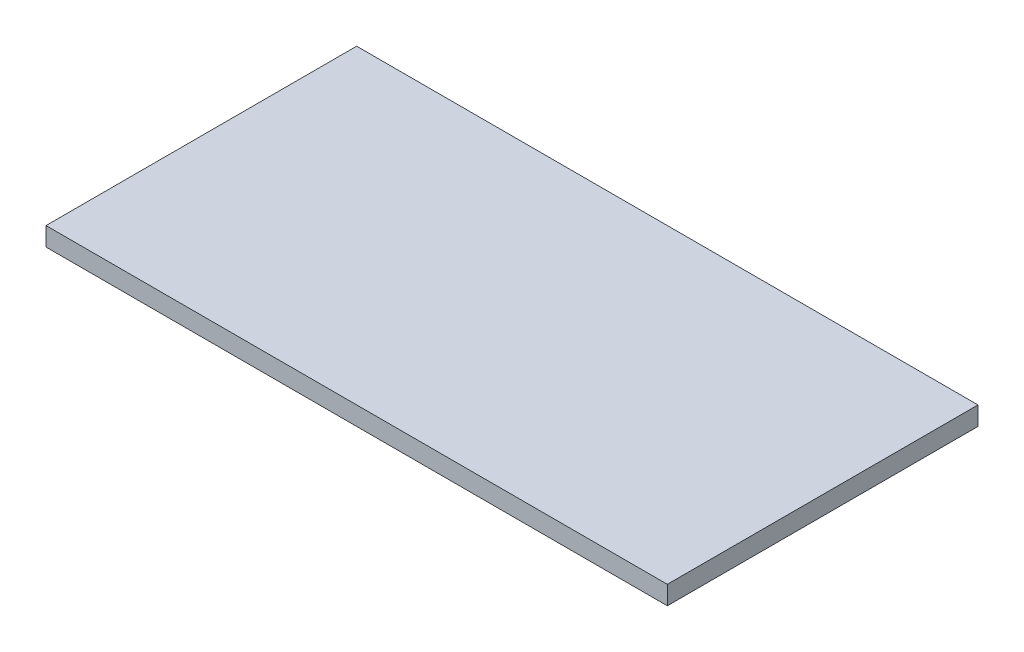
SolidWorks part; units mm, degrees
material "Recycled EPS"
ref_plane "Front Plane" through (0, 0, 0) normal (0, 0, 1) x (1, 0, 0)
ref_plane "Top Plane" through (0, 0, 0) normal (0, 1, 0) x (1, 0, 0)
ref_plane "Right Plane" through (0, 0, 0) normal (1, 0, 0) x (0, 0, -1)
sketch "Sketch1" plane through (0, 0, 0) normal (0, 1, 0) x (1, 0, 0)
  line L1 (-500, 250) -> (500, 250)
  line L2 (-500, 250) -> (-500, -250)
  line L3 (-500, -250) -> (500, -250)
  line L4 (500, 250) -> (500, -250)
  line L5 (-500, 250) -> (500, -250) construction
  line L6 (-500, -250) -> (500, 250) construction
  point P0 (0, 0)
  dimension "D1" = 1000
  dimension "D2" = 500
extrude "Boss-Extrude1" add sketch "Sketch1" along normal blind 30
